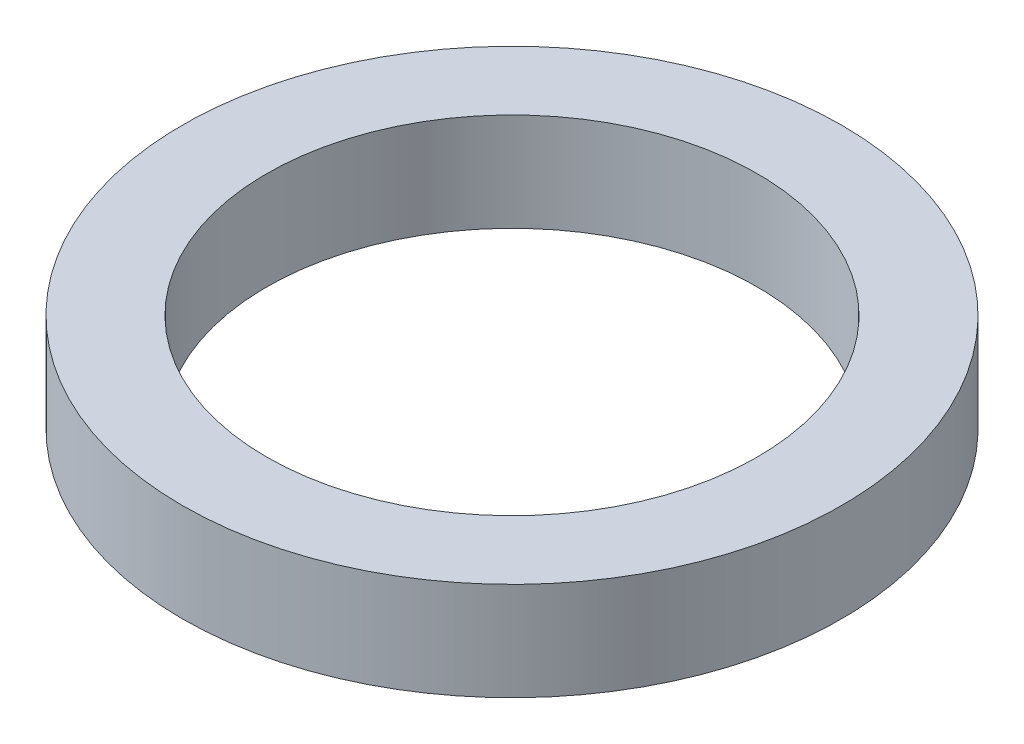
SolidWorks part; units mm, degrees
ref_plane "Front Plane" through (0, 0, 0) normal (0, 0, 1) x (1, 0, 0)
ref_plane "Top Plane" through (0, 0, 0) normal (0, 1, 0) x (1, 0, 0)
ref_plane "Right Plane" through (0, 0, 0) normal (1, 0, 0) x (0, 0, -1)
sketch "Sketch1" plane through (0, 0, 0) normal (0, 1, 0) x (1, 0, 0)
  circle A0 centre (0, 0) radius 17.5
  circle A1 centre (0, 0) radius 23.5
  dimension "D1" = 35
  dimension "D2" = 47
extrude "Boss-Extrude1" add sketch "Sketch1" along normal blind 7
